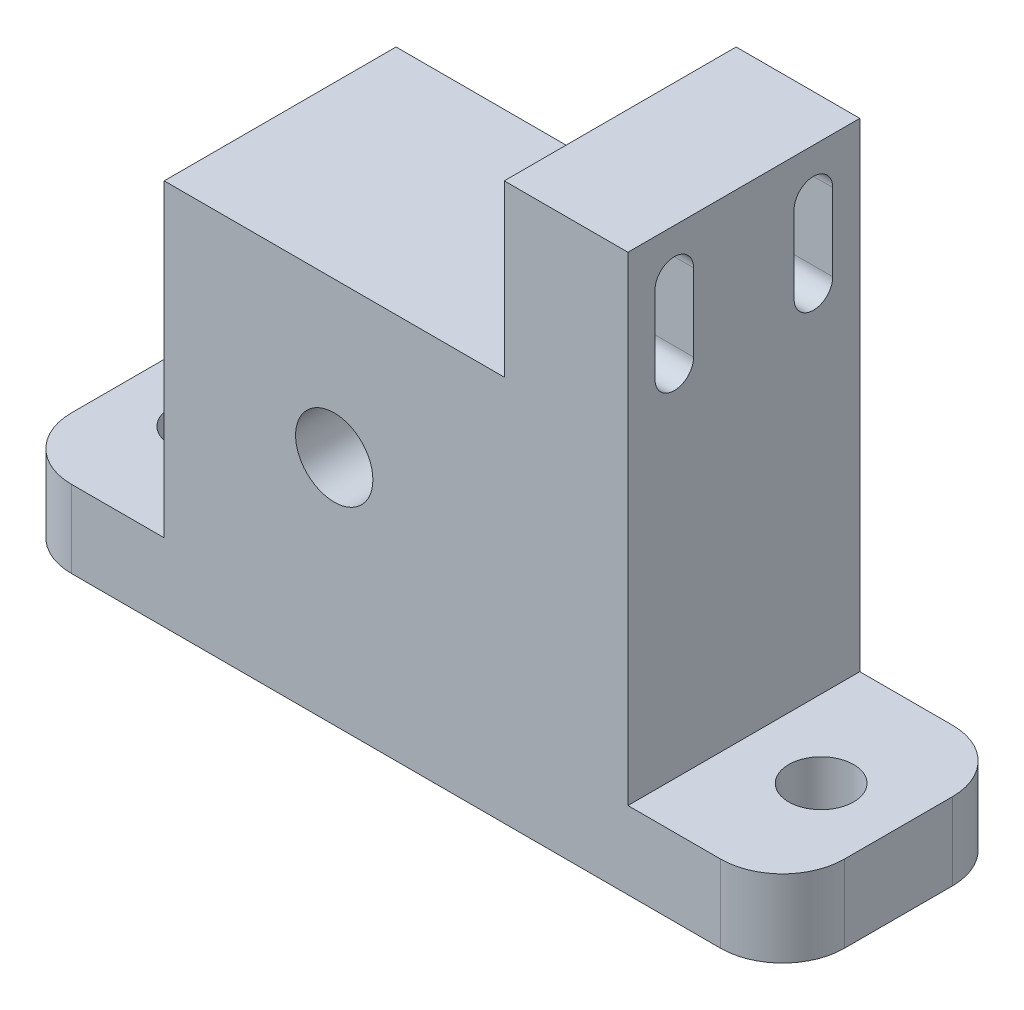
SolidWorks part; units mm, degrees
ref_plane "Plan de face" through (0, 0, 0) normal (0, 0, 1) x (1, 0, 0)
ref_plane "Plan de dessus" through (0, 0, 0) normal (0, 1, 0) x (1, 0, 0)
ref_plane "Plan de droite" through (0, 0, 0) normal (1, 0, 0) x (0, 0, -1)
sketch "Esquisse2" plane through (0, 0, 0) normal (0, 1, 0) x (1, 0, 0)
  line L1 (-15, 7.5) -> (15, 7.5)
  line L2 (-15, 7.5) -> (-15, -7.5)
  line L3 (-15, -7.5) -> (15, -7.5)
  line L4 (15, 7.5) -> (15, -7.5)
  line L5 (-15, 7.5) -> (15, -7.5) construction
  line L6 (-15, -7.5) -> (15, 7.5) construction
  point P0 (0, 0)
  dimension "D1" = 30
  dimension "D2" = 15
extrude "Boss.-Extru.1" add sketch "Esquisse2" along normal blind 25
sketch "Esquisse3" plane through (0, 25, 0) normal (0, 1, 0) x (1, 0, 0)
  line L0 (-15, -7.5) -> (15, -7.5) construction
  line L1 (15, 7.5) -> (7, 7.5)
  line L2 (15, 7.5) -> (15, -7.5)
  line L3 (15, -7.5) -> (7, -7.5)
  line L4 (7, 7.5) -> (7, -7.5)
  dimension "D1" = 8
extrude "Boss.-Extru.2" add sketch "Esquisse3" along normal blind 11
sketch "Esquisse4" plane through (0, 0, 7.5) normal (0, 0, 1) x (1, 0, 0)
  line L0 (-15, 25) -> (7, 25) construction
  line L1 (-15, 0) -> (15, 0) construction
  circle A0 centre (-4, 15) radius 2.5
  point P5 (-4, 25)
  dimension "D1" = 5
  dimension "D2" = 15
extrude "Enlèv. mat.-Extru.1" cut sketch "Esquisse4" against normal up to next
sketch "Esquisse5" plane through (7, 0, 0) normal (-1, 0, 0) x (0, 0, 1)
  line L0 (4.5, 33) -> (4.5, 28) construction
  line L1 (5.75, 33) -> (5.75, 28)
  line L2 (3.25, 33) -> (3.25, 28)
  line L3 (-4.5, 33) -> (-4.5, 28) construction
  line L4 (-3.25, 33) -> (-3.25, 28)
  line L5 (-5.75, 33) -> (-5.75, 28)
  line L6 (-7.5, 25) -> (7.5, 25) construction
  line L7 (-4.5, 30.5) -> (4.5, 30.5) construction
  arc A0 (5.75, 33) -> (3.25, 33) centre (4.5, 33) ccw
  arc A1 (3.25, 28) -> (5.75, 28) centre (4.5, 28) ccw
  arc A2 (-3.25, 33) -> (-5.75, 33) centre (-4.5, 33) ccw
  arc A3 (-5.75, 28) -> (-3.25, 28) centre (-4.5, 28) ccw
  point P2 (4.5, 30.5)
  point P7 (-4.5, 30.5)
  point P16 (0, 30.5)
  dimension "D2" = 1.25
  dimension "D1" = 5
  dimension "D3" = 3
  dimension "D4" = 9
extrude "Enlèv. mat.-Extru.2" cut sketch "Esquisse5" against normal up to next
sketch "Esquisse7" plane through (0, 0, 0) normal (0, -1, 0) x (1, 0, 0)
  line L0 (-15, 7.5) -> (15, 7.5) construction
  line L1 (-25, -7.5) -> (25, -7.5)
  line L2 (-25, -7.5) -> (-25, 7.5)
  line L3 (-25, 7.5) -> (25, 7.5)
  line L4 (25, -7.5) -> (25, 7.5)
  line L5 (-25, -7.5) -> (25, 7.5) construction
  line L6 (-25, 7.5) -> (25, -7.5) construction
  circle A0 centre (20, 0) radius 2.1
  circle A1 centre (-20, 0) radius 2.1
  point P0 (0, 0)
  dimension "D4" = 4.2
  dimension "D1" = 50
  dimension "D2" = 5
  dimension "D3" = 5
extrude "Boss.-Extru.4" add sketch "Esquisse7" against normal blind 5
fillet "Congé2" radius 4 4 edges at (25, 2.5, 7.5) (25, 2.5, -7.5) (-25, 2.5, -7.5) (-25, 2.5, 7.5)
equation "\"D2@Esquisse5\"=2.5/2"
equation "\"D3@Esquisse7\"=\"D2@Esquisse7\""
